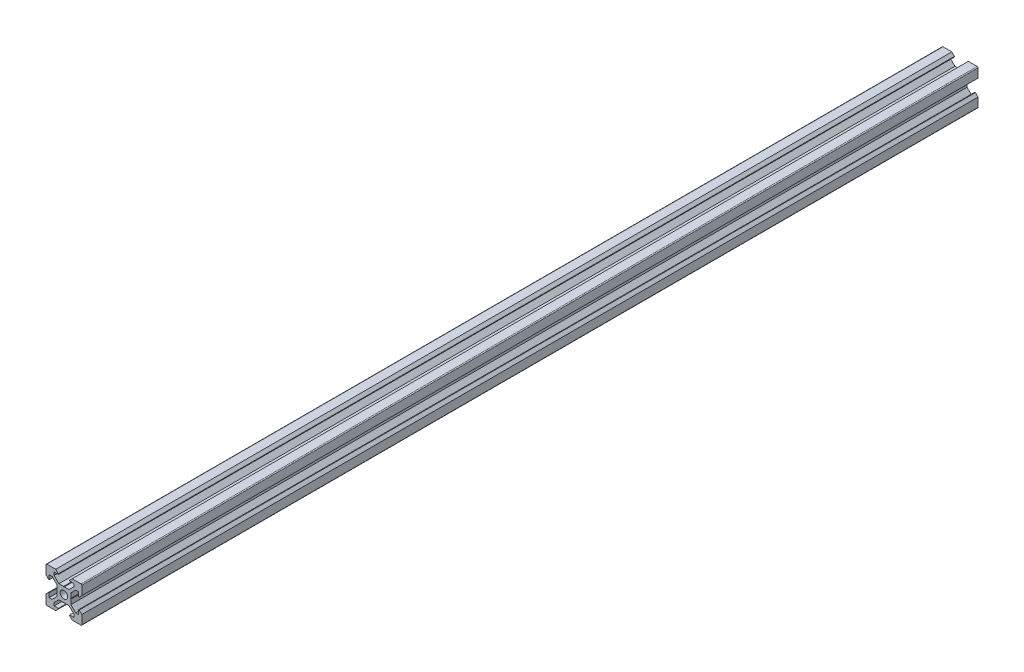
SolidWorks part; units mm, degrees
material "6061-T6 (SS)"
ref_plane "Front Plane" through (0, 0, 0) normal (0, 0, 1) x (1, 0, 0)
ref_plane "Top Plane" through (0, 0, 0) normal (0, 1, 0) x (1, 0, 0)
ref_plane "Right Plane" through (0, 0, 0) normal (1, 0, 0) x (0, 0, -1)
sketch "Sketch1" plane through (0, 0, 0) normal (0, 0, 1) x (1, 0, 0)
  line L1 (9.5, -10) -> (-9.5, -10)
  line L2 (10, -9.5) -> (10, 9.5)
  line L3 (9.5, 10) -> (-9.5, 10)
  line L4 (-10, -9.5) -> (-10, 9.5)
  line L5 (10, -10) -> (-10, 10) construction
  line L6 (10, 10) -> (-10, -10) construction
  circle A0 centre (0, 0) radius 2.1
  arc A1 (-9.5, 10) -> (-10, 9.5) centre (-9.5, 9.5) ccw
  arc A2 (10, 9.5) -> (9.5, 10) centre (9.5, 9.5) ccw
  arc A3 (9.5, -10) -> (10, -9.5) centre (9.5, -9.5) ccw
  arc A4 (-9.5, -10) -> (-10, -9.5) centre (-9.5, -9.5) cw
  point P0 (0, 0)
  line B0 (0, 0) -> (0, 10) construction
  line B1 (0, 3.69) -> (-0.21, 3.9)
  line B2 (-0.21, 3.9) -> (-2.8393, 3.9)
  line B3 (-2.8393, 3.9) -> (-5.5, 6.5607)
  line B4 (-5.5, 6.5607) -> (-5.5, 8.2)
  line B5 (-5.5, 8.2) -> (-3.125, 8.2)
  line B6 (-3.125, 8.2) -> (-3.125, 8.545)
  line B7 (-3.125, 8.545) -> (-4.58, 10)
  line B8 (-4.58, 10) -> (4.58, 10)
  line B9 (0, 0) -> (-5.9132, 5.9132) construction
  line B10 (3.125, 8.545) -> (4.58, 10)
  line B11 (3.125, 8.2) -> (3.125, 8.545)
  line B12 (5.5, 8.2) -> (3.125, 8.2)
  line B13 (5.5, 6.5607) -> (5.5, 8.2)
  line B14 (2.8393, 3.9) -> (5.5, 6.5607)
  line B15 (0.21, 3.9) -> (2.8393, 3.9)
  line B16 (0, 3.69) -> (0.21, 3.9)
  line B17 (0, 0) -> (-10, 0) construction
  line B18 (-3.69, 0) -> (-3.9, -0.21)
  line B19 (-3.9, -0.21) -> (-3.9, -2.8393)
  line B20 (-3.9, -2.8393) -> (-6.5607, -5.5)
  line B21 (-6.5607, -5.5) -> (-8.2, -5.5)
  line B22 (-8.2, -5.5) -> (-8.2, -3.125)
  line B23 (-8.2, -3.125) -> (-8.545, -3.125)
  line B24 (-8.545, -3.125) -> (-10, -4.58)
  line B25 (-10, -4.58) -> (-10, 4.58)
  line B26 (0, 0) -> (-5.9132, -5.9132) construction
  line B27 (-8.545, 3.125) -> (-10, 4.58)
  line B28 (-8.2, 3.125) -> (-8.545, 3.125)
  line B29 (-8.2, 5.5) -> (-8.2, 3.125)
  line B30 (-6.5607, 5.5) -> (-8.2, 5.5)
  line B31 (-3.9, 2.8393) -> (-6.5607, 5.5)
  line B32 (-3.9, 0.21) -> (-3.9, 2.8393)
  line B33 (-3.69, 0) -> (-3.9, 0.21)
  line B34 (0, 0) -> (0, -10) construction
  line B35 (0, -3.69) -> (0.21, -3.9)
  line B36 (0.21, -3.9) -> (2.8393, -3.9)
  line B37 (2.8393, -3.9) -> (5.5, -6.5607)
  line B38 (5.5, -6.5607) -> (5.5, -8.2)
  line B39 (5.5, -8.2) -> (3.125, -8.2)
  line B40 (3.125, -8.2) -> (3.125, -8.545)
  line B41 (3.125, -8.545) -> (4.58, -10)
  line B42 (4.58, -10) -> (-4.58, -10)
  line B43 (0, 0) -> (5.9132, -5.9132) construction
  line B44 (-3.125, -8.545) -> (-4.58, -10)
  line B45 (-3.125, -8.2) -> (-3.125, -8.545)
  line B46 (-5.5, -8.2) -> (-3.125, -8.2)
  line B47 (-5.5, -6.5607) -> (-5.5, -8.2)
  line B48 (-2.8393, -3.9) -> (-5.5, -6.5607)
  line B49 (-0.21, -3.9) -> (-2.8393, -3.9)
  line B50 (0, -3.69) -> (-0.21, -3.9)
  line B51 (0, 0) -> (10, 0) construction
  line B52 (3.69, 0) -> (3.9, 0.21)
  line B53 (3.9, 0.21) -> (3.9, 2.8393)
  line B54 (3.9, 2.8393) -> (6.5607, 5.5)
  line B55 (6.5607, 5.5) -> (8.2, 5.5)
  line B56 (8.2, 5.5) -> (8.2, 3.125)
  line B57 (8.2, 3.125) -> (8.545, 3.125)
  line B58 (8.545, 3.125) -> (10, 4.58)
  line B59 (10, 4.58) -> (10, -4.58)
  line B60 (0, 0) -> (5.9132, 5.9132) construction
  line B61 (8.545, -3.125) -> (10, -4.58)
  line B62 (8.2, -3.125) -> (8.545, -3.125)
  line B63 (8.2, -5.5) -> (8.2, -3.125)
  line B64 (6.5607, -5.5) -> (8.2, -5.5)
  line B65 (3.9, -2.8393) -> (6.5607, -5.5)
  line B66 (3.9, -0.21) -> (3.9, -2.8393)
  line B67 (3.69, 0) -> (3.9, -0.21)
  dimension "D1" = 4.2
  dimension "D3" = 0.5
  dimension "D2" = 20
sketch_block_instance "V Slot 1-4"
sketch_block "V Slot 1" parameters "D1"=10, "D2"=11, "D3"=4.3, "D4"=1.8, "D5"=0.21, "D6"=45, "D7"=9.16, "D8"=1.5, "D9"=6.25
sketch_block_instance "V Slot 1-5"
sketch_block_instance "V Slot 1-6"
sketch_block_instance "V Slot 1-7"
extrude "Boss-Extrude1" add sketch "Sketch1" along normal blind 500 contours B67 B52 B53 B54 B55 B56 B57 B58 L2 A2 L3 B10 B11 B12 B13 B14 B15 B16 B1 B2 B3 B4 B5 B6 B7 A1 L4 B27 B28 B29 B30 B31 B32 B33 B18 B19 B20 B21 B22 B23 B24 A4 L1 B44 B45 B46 B47 B48 B49
